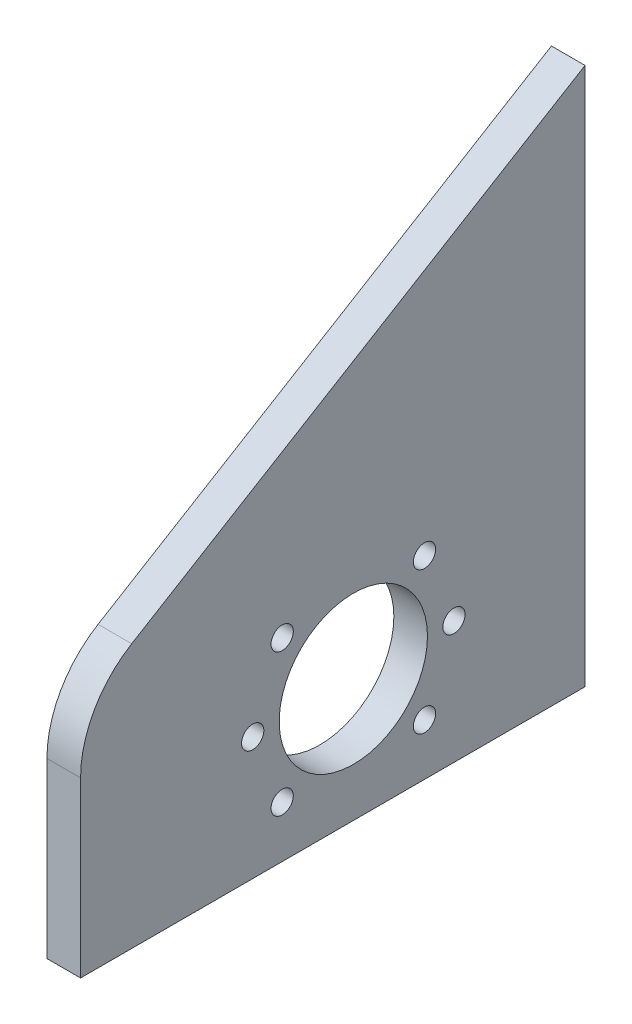
SolidWorks part; units mm, degrees
ref_plane "Front Plane" through (0, 0, 0) normal (0, 0, 1) x (1, 0, 0)
ref_plane "Top Plane" through (0, 0, 0) normal (0, 1, 0) x (1, 0, 0)
ref_plane "Right Plane" through (0, 0, 0) normal (1, 0, 0) x (0, 0, -1)
sketch "Sketch1" plane through (0, 0, 0) normal (1, 0, 0) x (0, 0, -1)
  line L0 (0, 0) -> (-95.25, 0)
  line L1 (-95.25, 0) -> (-95.25, 44)
  line L2 (-95.25, 44) -> (0, 101.6)
  line L3 (0, 101.6) -> (0, 0)
  dimension "D1" = 95.25
  dimension "D2" = 101.6
  dimension "D3" = 44
extrude "Boss-Extrude1" add sketch "Sketch1" against normal blind 6.35
fillet "Fillet1" radius 20 1 edges at (-3.175, 44, 95.25)
sketch "Sketch2" plane through (0, 0, 0) normal (1, 0, 0) x (0, 0, -1)
  line L0 (-95.25, 0) -> (0, 0) construction
  line L1 (-95.25, 32.7219) -> (-95.25, 0) construction
  circle A0 centre (-43.75, 23.17) radius 14
  dimension "D3" = 28
  dimension "D1" = 23.17
  dimension "D2" = 51.5
extrude "Cut-Extrude1" cut sketch "Sketch2" against normal blind 6.35
sketch "Sketch3" plane through (0, 0, 0) normal (1, 0, 0) x (0, 0, -1)
  circle A0 centre (-57.185, 36.605) radius 2.1
  circle A1 centre (-62.75, 23.17) radius 2.1
  circle A2 centre (-57.185, 9.735) radius 2.1
  circle A3 centre (-30.315, 9.735) radius 2.1
  circle A4 centre (-24.75, 23.17) radius 2.1
  circle A5 centre (-30.315, 36.605) radius 2.1
  point P0 (-57.185, 36.605)
  point P1 (-62.75, 23.17)
  point P3 (-57.185, 9.735)
  point P7 (-30.315, 9.735)
  point P9 (-24.75, 23.17)
  point P11 (-30.315, 36.605)
  dimension "D1" = 4.2
  dimension "D2" = 32.5
  dimension "D3" = 38.065
  dimension "D4" = 64.935
  dimension "D5" = 70.5
  dimension "D6" = 64.995
  dimension "D7" = 78.43
  dimension "D8" = 91.865
extrude "Cut-Extrude2" cut sketch "Sketch3" against normal blind 10
